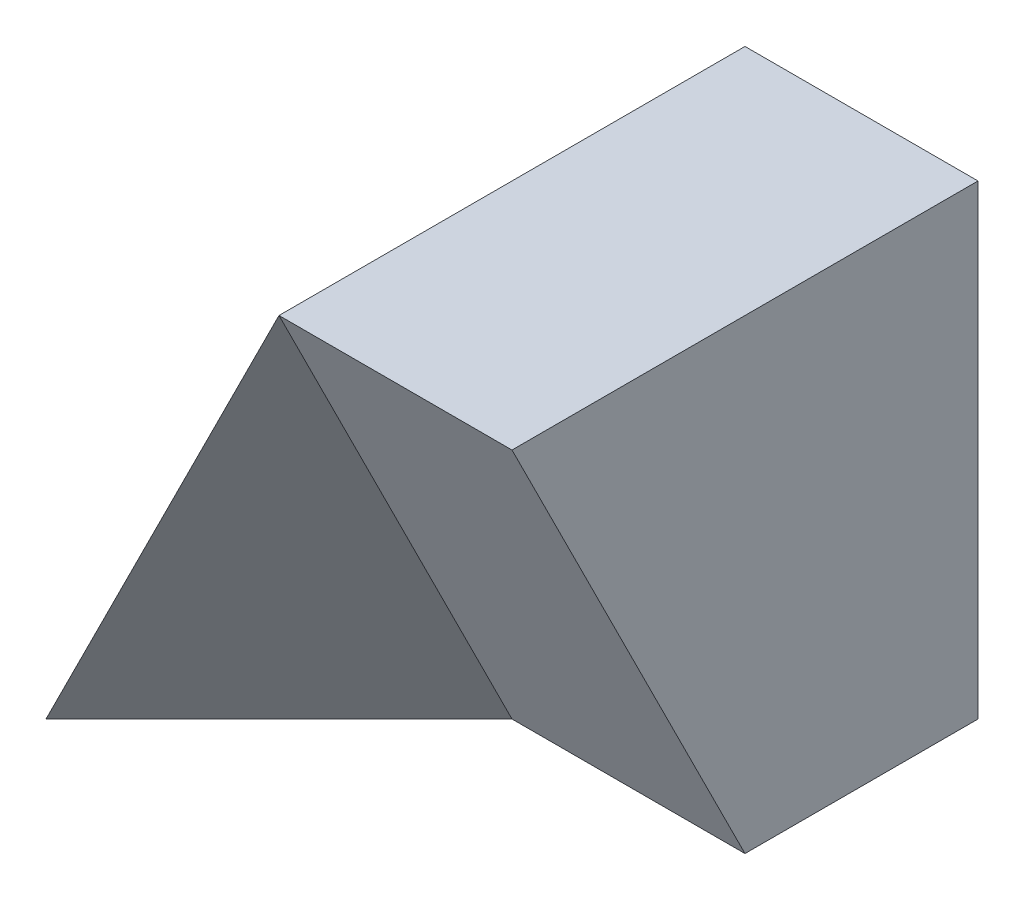
SolidWorks part; units mm, degrees
ref_plane "Front Plane" through (0, 0, 0) normal (0, 0, 1) x (1, 0, 0)
ref_plane "Top Plane" through (0, 0, 0) normal (0, 1, 0) x (1, 0, 0)
ref_plane "Right Plane" through (0, 0, 0) normal (1, 0, 0) x (0, 0, -1)
sketch "Sketch1" plane through (0, 0, 0) normal (0, 0, 1) x (1, 0, 0)
  line L1 (0, 0) -> (40, 0)
  line L2 (0, 0) -> (0, 40)
  line L3 (0, 40) -> (40, 40)
  line L4 (40, 0) -> (40, 40)
  dimension "D1" = 40
  dimension "D2" = 40
extrude "Boss-Extrude1" add sketch "Sketch1" along normal blind 40
sketch "Sketch2" plane through (0, 0, 40) normal (0, 0, 1) x (1, 0, 0)
  line L0 (0, 0) -> (20, 40)
  line L1 (40, 40) -> (0, 40) construction
  line L2 (20, 40) -> (0, 40)
  line L3 (0, 40) -> (0, 0)
extrude "Cut-Extrude1" cut sketch "Sketch2" against normal blind 40
sketch "Sketch3" plane through (40, 0, 0) normal (1, 0, 0) x (0, 0, -1)
  line L0 (-20, 0) -> (-40, 40)
  line L2 (-40, 0) -> (0, 0) construction
  line L3 (-40, 40) -> (-40, 0)
  line L4 (-40, 0) -> (-20, 0)
extrude "Cut-Extrude3" cut sketch "Sketch3" against normal blind 20
ref_plane "Plane1" through (17.7778, -8.8889, 17.7778) normal (0.6667, -0.3333, 0.6667) x (0.7454, 0.2981, -0.5963)
sketch "Sketch5" plane through (17.7778, -8.8889, 17.7778) normal (0.6667, -0.3333, 0.6667) x (0.7454, 0.2981, -0.5963)
  line L0 (2.9814, 53.6656) -> (2.9814, 8.9443)
  line L1 (2.9814, 8.9443) -> (-23.8514, 17.8885)
  line L2 (-23.8514, 17.8885) -> (2.9814, 53.6656)
extrude "Cut-Extrude4" cut sketch "Sketch5" along normal blind 20
